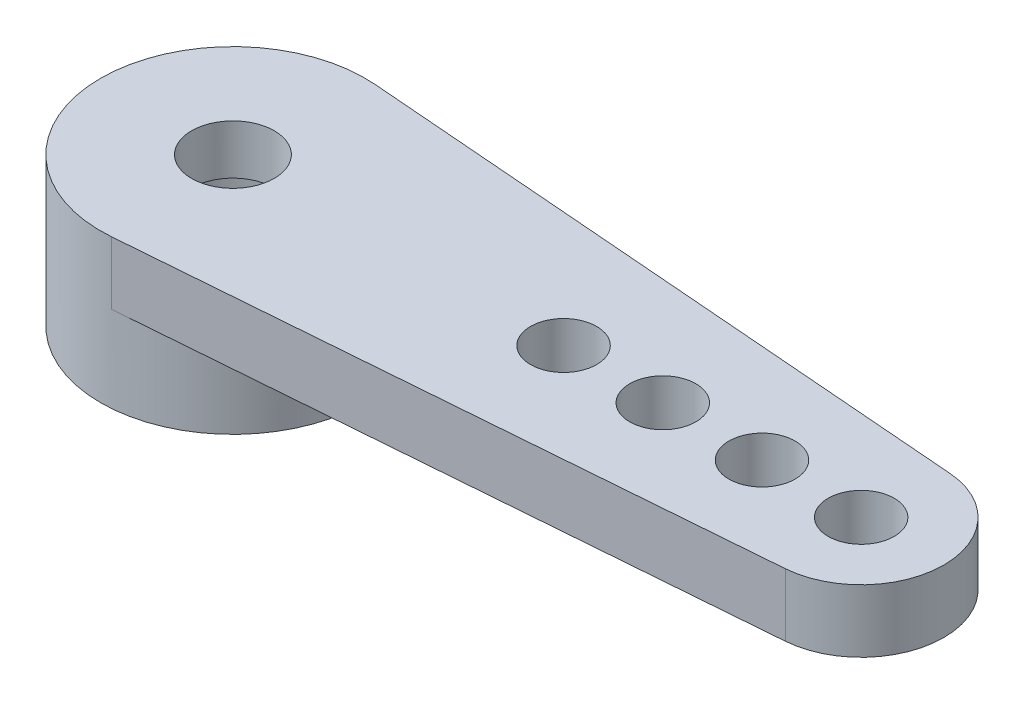
SolidWorks part; units mm, degrees
material "普通碳钢"
ref_plane "前视基准面" through (0, 0, 0) normal (0, 0, 1) x (1, 0, 0)
ref_plane "上视基准面" through (0, 0, 0) normal (0, 1, 0) x (1, 0, 0)
ref_plane "右视基准面" through (0, 0, 0) normal (1, 0, 0) x (0, 0, -1)
other "Configuration Table"
sketch "草图1" plane through (0, 0, 0) normal (0, 1, 0) x (1, 0, 0)
  circle A0 centre (0, 0) radius 4
  circle A1 centre (0, 0) radius 1.25
  dimension "D1" = 8
  dimension "D2" = 2.5
extrude "凸台-拉伸1" add sketch "草图1" along normal blind 4.5
sketch "草图2" plane through (0, 4.5, 0) normal (0, 1, 0) x (1, 0, 0)
  line L0 (0, 0) -> (19, 0) construction
  line L1 (0.3158, 3.9875) -> (19.1974, 2.4922)
  line L2 (0.3158, -3.9875) -> (19.1974, -2.4922)
  circle A0 centre (19, 0) radius 2.5
  circle A1 centre (10, 0) radius 1
  circle A2 centre (13, 0) radius 1
  circle A3 centre (16, 0) radius 1
  circle A4 centre (19, 0) radius 1
  circle A5 centre (0, 0) radius 4 construction
  circle A6 centre (0, 0) radius 4
  point P13 (21.5, 0)
  dimension "D5" = 2
  dimension "D6" = 2
  dimension "D7" = 2
  dimension "D8" = 2
  dimension "D1" = 19
  dimension "D2" = 10
  dimension "D3" = 3
  dimension "D4" = 3
  dimension "D9" = 21.5
extrude "凸台-拉伸2" add sketch "草图2" against normal blind 1.9
sketch "草图3" plane through (0, 0, 0) normal (0, -1, 0) x (1, 0, 0)
  circle A0 centre (0, 0) radius 2.4
  dimension "D1" = 4.8
extrude "切除-拉伸1" cut sketch "草图3" against normal blind 3
